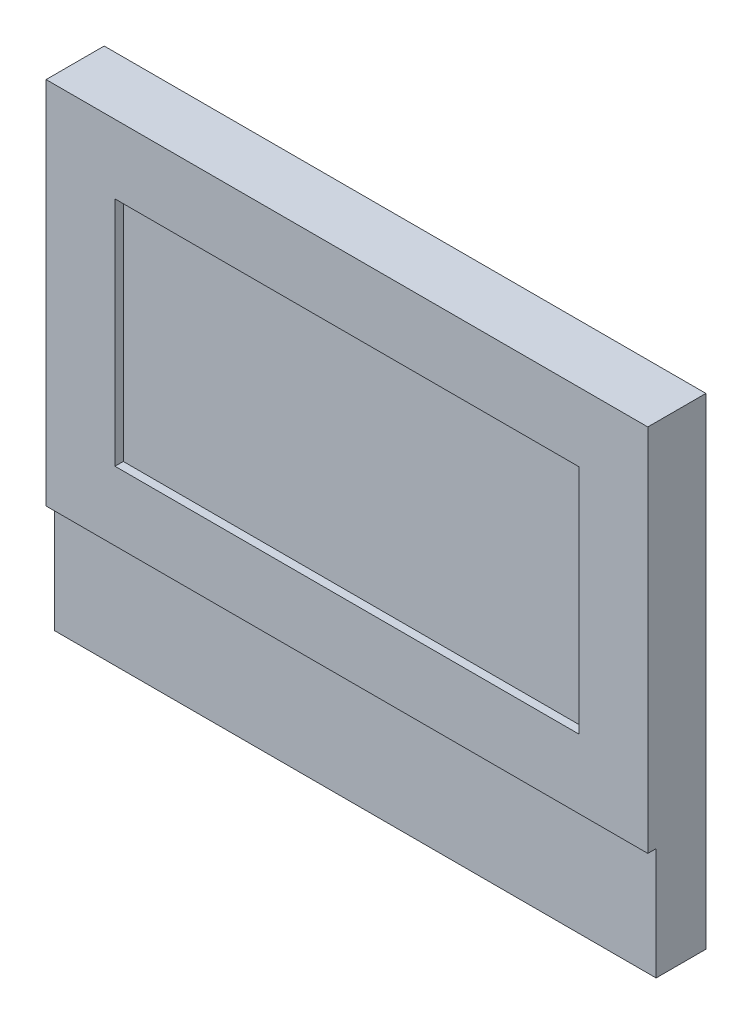
SolidWorks part; units mm, degrees
ref_plane "Front Plane" through (0, 0, 0) normal (0, 0, 1) x (1, 0, 0)
ref_plane "Top Plane" through (0, 0, 0) normal (0, 1, 0) x (1, 0, 0)
ref_plane "Right Plane" through (0, 0, 0) normal (1, 0, 0) x (0, 0, -1)
sketch "Sketch1" plane through (0, 0, 0) normal (0, 0, 1) x (1, 0, 0)
  line L1 (-72.5, 58) -> (72.5, 58)
  line L2 (-72.5, 58) -> (-72.5, -58)
  line L3 (-72.5, -58) -> (72.5, -58)
  line L4 (72.5, 58) -> (72.5, -58)
  line L5 (-72.5, 58) -> (72.5, -58) construction
  line L6 (-72.5, -58) -> (72.5, 58) construction
  point P0 (0, 0)
  dimension "D1" = 145
  dimension "D2" = 116
extrude "Boss-Extrude1" add sketch "Sketch1" along normal blind 12
sketch "Sketch2" plane through (0, 0, 12) normal (0, 0, 1) x (1, 0, 0)
  line L0 (0, 41.4) -> (0, -62.0117) construction
  line L3 (-55.9, 41.4) -> (55.9, 41.4)
  line L4 (-55.9, 41.4) -> (-55.9, -14.4)
  line L5 (-55.9, -14.4) -> (55.9, -14.4)
  line L6 (55.9, 41.4) -> (55.9, -14.4)
  line L7 (-72.5, 58) -> (-72.5, -31)
  line L8 (-72.5, -31) -> (72.5, -31)
  line L9 (72.5, 58) -> (72.5, -31)
  line L10 (-72.5, 58) -> (72.5, 58)
  line L11 (72.5, 58) -> (-72.5, 58) construction
  point P2 (0, 41.4)
  point P3 (0, 56.293)
  point P9 (0, 0)
  dimension "D1" = 111.8
  dimension "D2" = 55.8
  dimension "D4" = 16.6
extrude "Boss-Extrude2" add sketch "Sketch2" along normal blind 2 contours L0 L3 L4 L5 | L3 L0 L5 L6 | L7 L8 L9 L10
